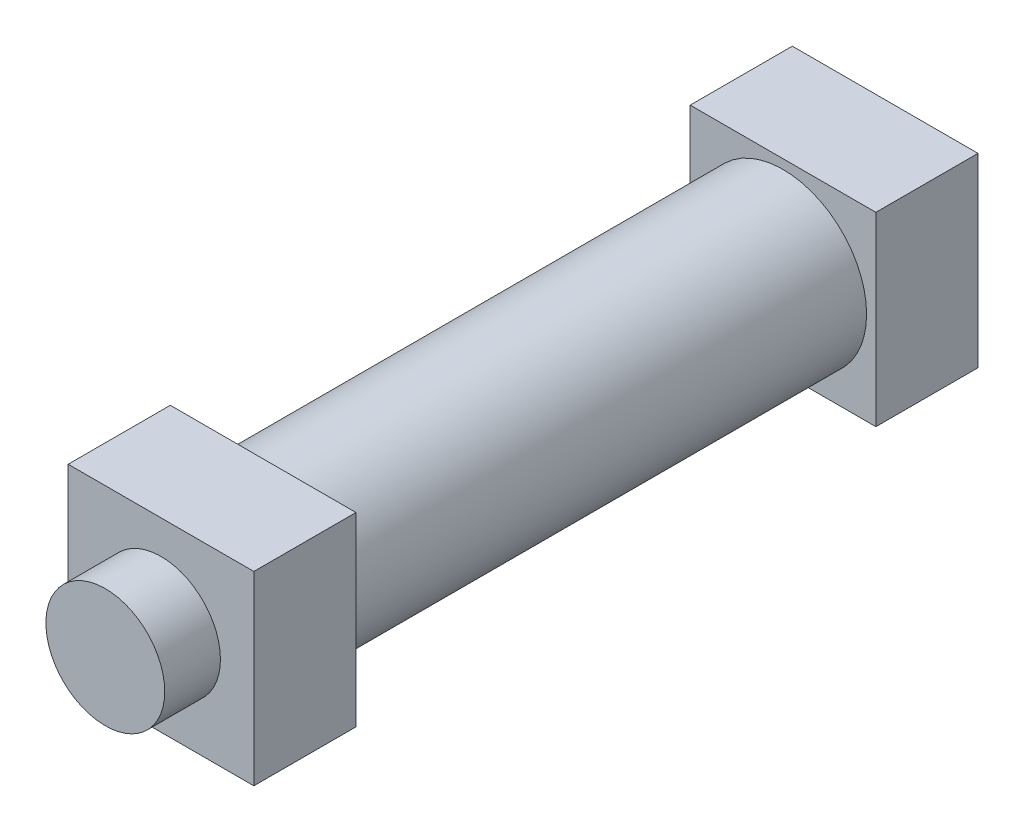
SolidWorks part; units mm, degrees
ref_plane "Front Plane" through (0, 0, 0) normal (0, 0, 1) x (1, 0, 0)
ref_plane "Top Plane" through (0, 0, 0) normal (0, 1, 0) x (1, 0, 0)
ref_plane "Right Plane" through (0, 0, 0) normal (1, 0, 0) x (0, 0, -1)
sketch "Sketch1" plane through (0, 0, 0) normal (0, 0, 1) x (1, 0, 0)
  line L1 (0, 0) -> (50, 0)
  line L2 (0, 0) -> (0, 50)
  line L3 (0, 50) -> (50, 50)
  line L4 (50, 0) -> (50, 50)
  dimension "D1" = 50
extrude "Boss-Extrude1" add sketch "Sketch1" along normal blind 27.5
sketch "Sketch3" plane through (0, 0, 27.5) normal (0, 0, 1) x (1, 0, 0)
  line L0 (0, 0) -> (50, 50) construction
  circle A0 centre (25, 25) radius 22.5
  point P6 (25, 25)
  dimension "D1" = 45
extrude "Boss-Extrude2" add sketch "Sketch3" along normal blind 140
sketch "Sketch4" plane through (0, 0, 167.5) normal (0, 0, 1) x (1, 0, 0)
  line L1 (0, 0) -> (50, 0)
  line L2 (0, 0) -> (0, 50)
  line L3 (0, 50) -> (50, 50)
  line L4 (50, 0) -> (50, 50)
extrude "Boss-Extrude3" add sketch "Sketch4" along normal blind 27.5
sketch "Sketch5" plane through (0, 0, 195) normal (0, 0, 1) x (1, 0, 0)
  line L0 (0, 0) -> (50, 50) construction
  circle A0 centre (25, 25) radius 16
  dimension "D1" = 32
extrude "Boss-Extrude4" add sketch "Sketch5" along normal blind 15
